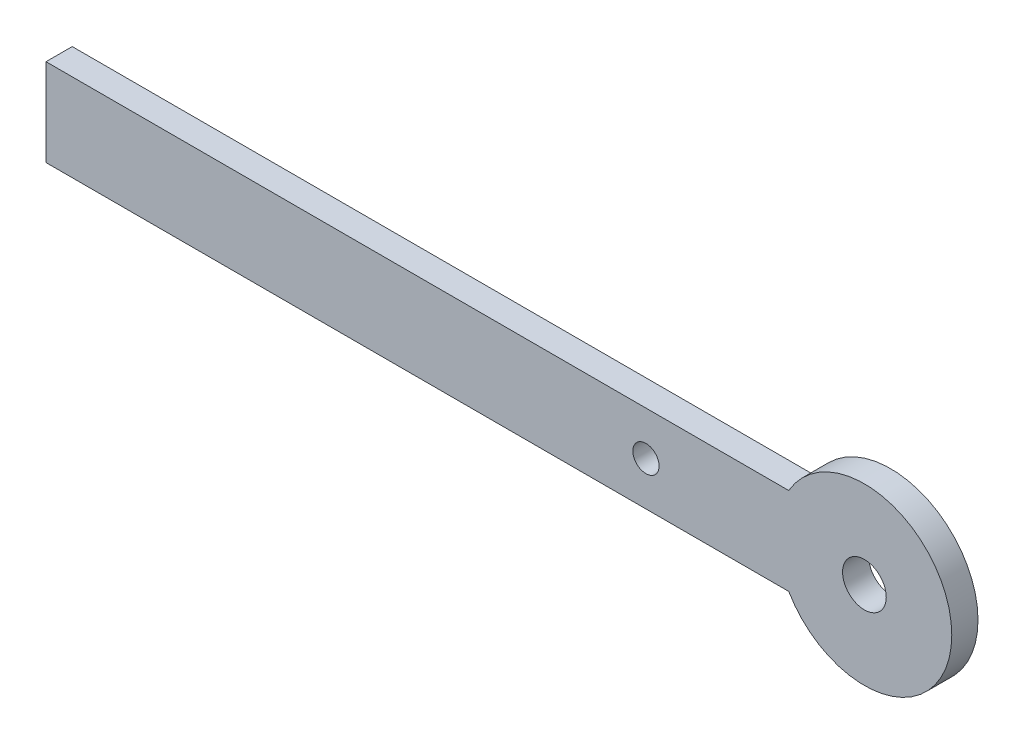
SolidWorks part; units mm, degrees
ref_plane "Front Plane" through (0, 0, 0) normal (0, 0, 1) x (1, 0, 0)
ref_plane "Top Plane" through (0, 0, 0) normal (0, 1, 0) x (1, 0, 0)
ref_plane "Right Plane" through (0, 0, 0) normal (1, 0, 0) x (0, 0, -1)
sketch "Sketch1" plane through (0, 0, 0) normal (0, 0, 1) x (1, 0, 0)
  line L0 (-93.6603, 5) -> (-8.6603, 5)
  line L1 (-93.6603, 5) -> (-93.6603, -5)
  line L2 (-93.6603, -5) -> (-8.6603, -5)
  line L3 (0, 0) -> (-66.4424, 0) construction
  arc A0 (-8.6603, -5) -> (-8.6603, 5) centre (0, 0) ccw
  circle A1 centre (0, 0) radius 2.5
  dimension "D1" = 20
  dimension "D2" = 5
  dimension "D3" = 5
  dimension "D4" = 5
  dimension "D5" = 85
extrude "Boss-Extrude1" add sketch "Sketch1" along normal blind 3
sketch "Sketch2" plane through (0, 0, 0) normal (0, 0, -1) x (-1, 0, 0)
  line L0 (0, 0) -> (0, 13.1896) construction
  line L1 (0, 0) -> (17.4591, 0) construction
  circle A1 centre (25, 0) radius 1.5
  dimension "D1" = 3
  dimension "D2" = 25
extrude "Cut-Extrude1" cut sketch "Sketch2" against normal blind 10
